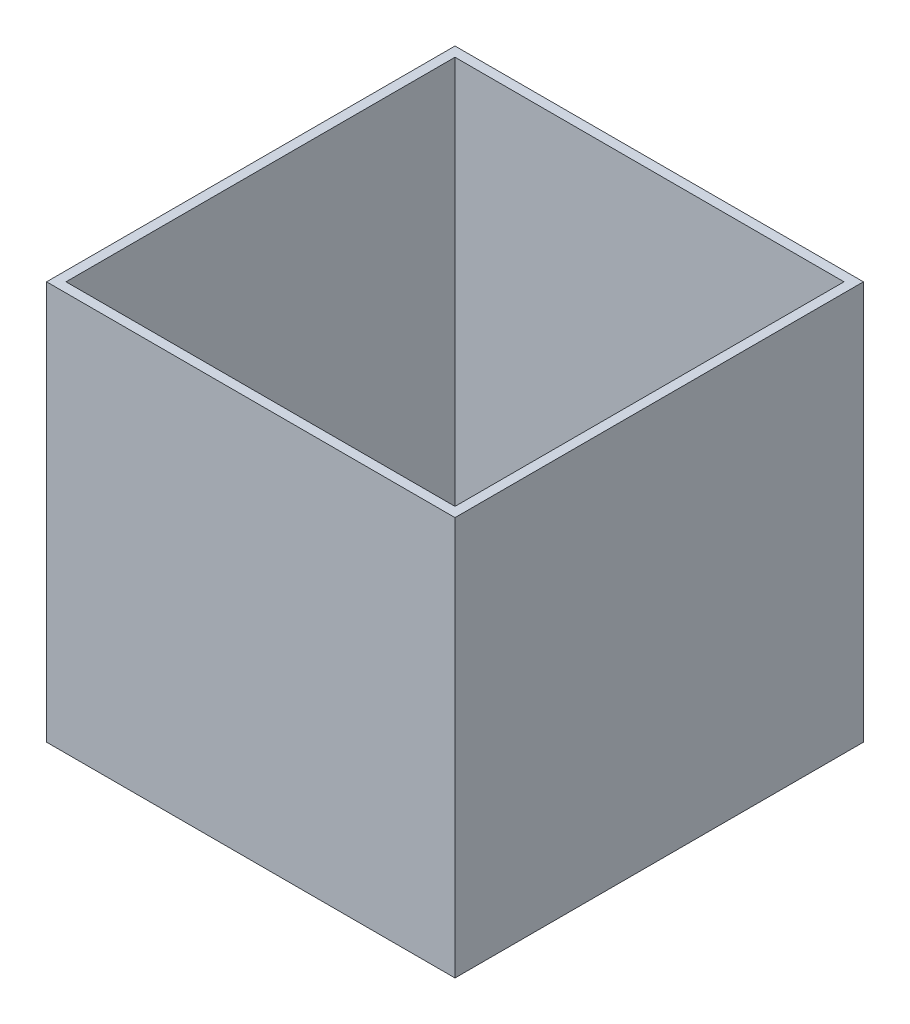
SolidWorks part; units mm, degrees
ref_plane "Front Plane" through (0, 0, 0) normal (0, 0, 1) x (1, 0, 0)
ref_plane "Top Plane" through (0, 0, 0) normal (0, 1, 0) x (1, 0, 0)
ref_plane "Right Plane" through (0, 0, 0) normal (1, 0, 0) x (0, 0, -1)
sketch "Sketch1" plane through (0, 0, 0) normal (0, 1, 0) x (1, 0, 0)
  line L1 (0, 0) -> (420, 0)
  line L2 (0, 0) -> (0, 420)
  line L3 (0, 420) -> (420, 420)
  line L4 (420, 0) -> (420, 420)
  dimension "D1" = 420
  dimension "D2" = 420
extrude "Boss-Extrude1" add sketch "Sketch1" along normal blind 10
sketch "Sketch2" plane through (0, 10, 0) normal (0, 1, 0) x (1, 0, 0)
  line L1 (0, 420) -> (420, 420)
  line L2 (0, 420) -> (0, 0)
  line L3 (0, 0) -> (420, 0)
  line L4 (420, 420) -> (420, 0)
  line L5 (10, 410) -> (410, 410)
  line L6 (10, 410) -> (10, 10)
  line L7 (10, 10) -> (410, 10)
  line L8 (410, 410) -> (410, 10)
  dimension "D1" = 10
  dimension "D2" = 10
  dimension "D3" = 400
  dimension "D4" = 400
extrude "Boss-Extrude2" add sketch "Sketch2" along normal blind 400
